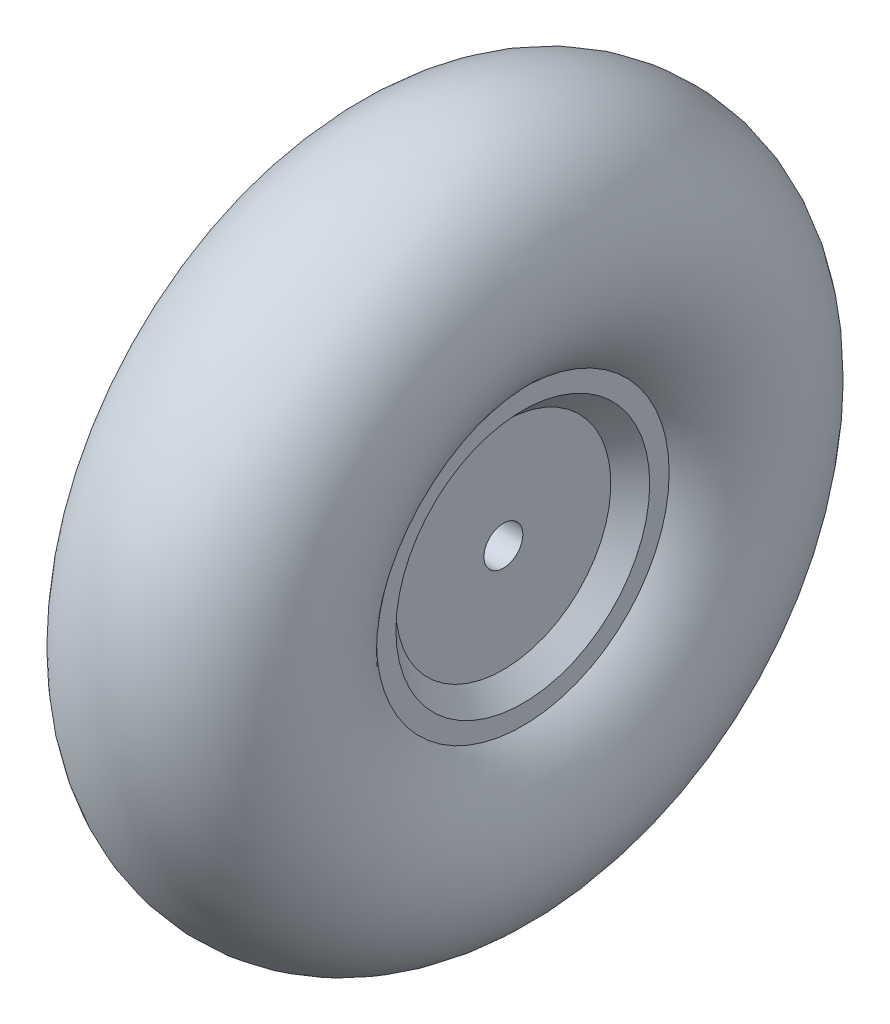
SolidWorks part; units mm, degrees
material "Rubber"
ref_plane "Front Plane" through (0, 0, 0) normal (0, 0, 1) x (1, 0, 0)
ref_plane "Top Plane" through (0, 0, 0) normal (0, 1, 0) x (1, 0, 0)
ref_plane "Right Plane" through (0, 0, 0) normal (1, 0, 0) x (0, 0, -1)
sketch "Sketch1" plane through (0, 0, 0) normal (0, 0, 1) x (1, 0, 0)
  line L0 (0, 23.7677) -> (0, -2.5465) construction
  line L1 (12.7, 23.901) -> (12.7, 20.726)
  line L2 (12.7, 20.726) -> (9.525, 17.551)
  line L3 (9.525, 17.551) -> (9.525, 3.175)
  line L4 (9.525, 3.175) -> (-9.525, 3.175)
  line L5 (-53.507, 0) -> (45.9358, 0) construction
  line L6 (-12.7, 23.901) -> (-12.7, 20.726)
  line L7 (-9.525, 17.551) -> (-9.525, 3.175)
  line L8 (-12.7, 20.726) -> (-9.525, 17.551)
  arc A0 (-12.7, 23.901) -> (12.7, 23.901) centre (0, 38.1) cw
  point P14 (0, 3.175)
  dimension "D3" = 19.05
  dimension "D4" = 9.525
  dimension "D5" = 3.175
  dimension "D6" = 45
  dimension "D7" = 3.175
  dimension "D1" = 6.35
  dimension "D2" = 76.2
revolve "Revolve1" add sketch "Sketch1" angle 360 about L5
equation "\"D2@Sketch1\"=4.5-(2*\"D3@Sketch1\")"
